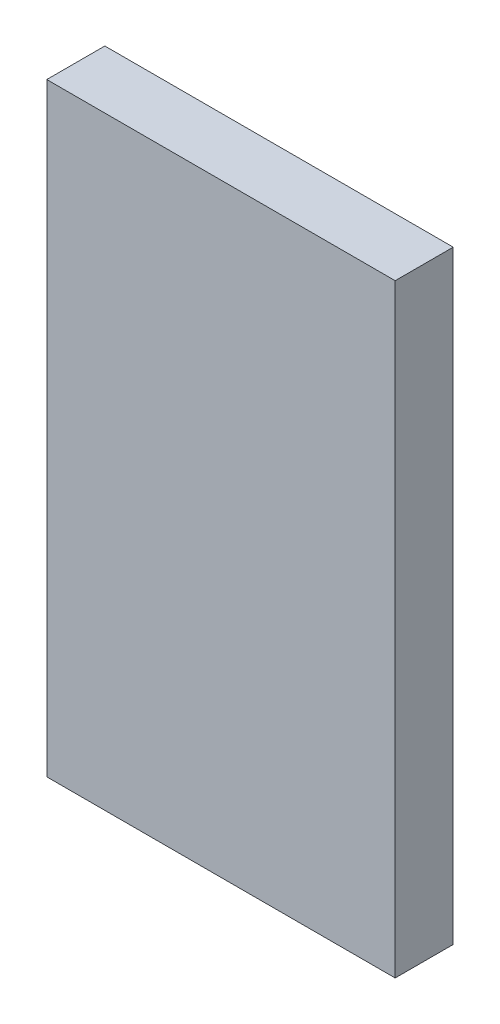
SolidWorks part; units mm, degrees
ref_plane "Front Plane" through (0, 0, 0) normal (1, 0, 0) x (0, 1, 0)
ref_plane "Top Plane" through (0, 0, 0) normal (0, 0, 1) x (0, 1, 0)
ref_plane "Right Plane" through (0, 0, 0) normal (0, 1, 0) x (-1, 0, 0)
sketch "Sketch1" plane through (0, 0, 0) normal (0, 0, 1) x (0, 1, 0)
  line L1 (0, 0) -> (26, 0)
  line L2 (0, 0) -> (0, 15)
  line L3 (0, 15) -> (26, 15)
  line L4 (26, 0) -> (26, 15)
  dimension "D1" = 26
  dimension "D2" = 15
extrude "Boss-Extrude1" add sketch "Sketch1" along normal blind 2.5
